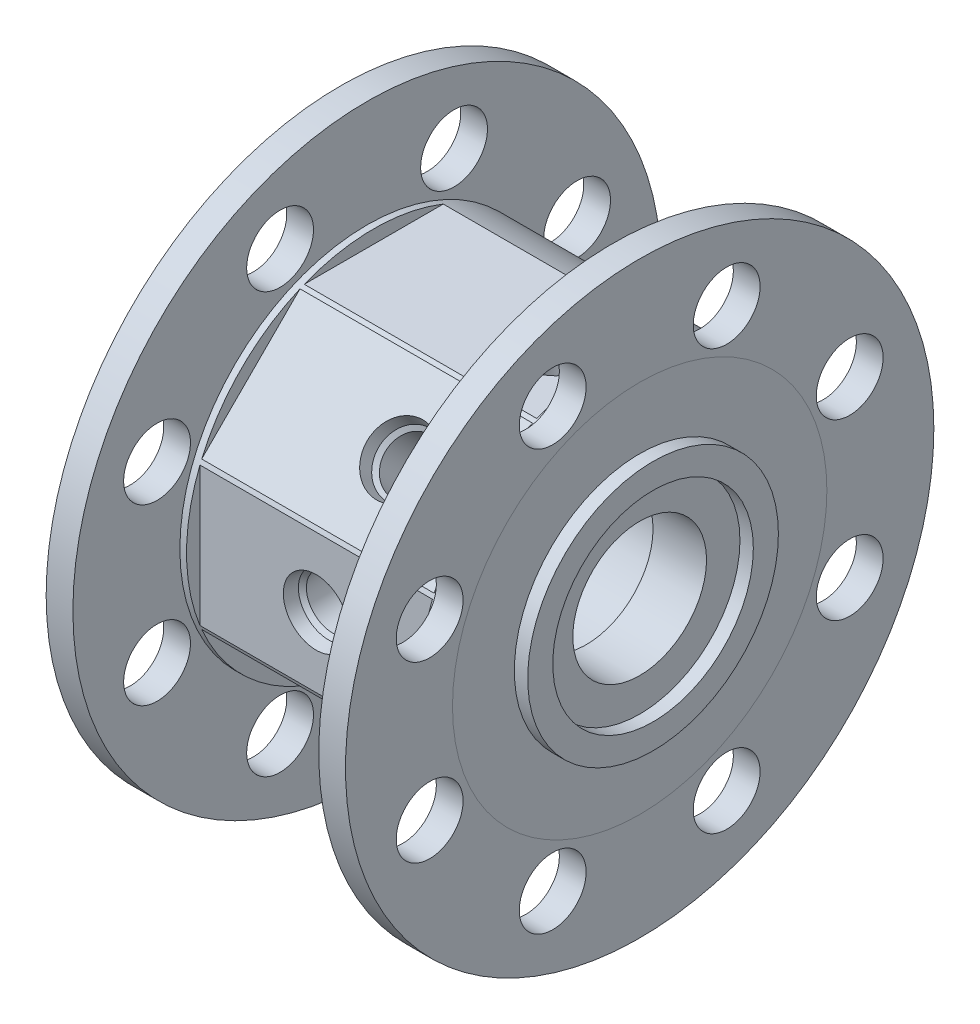
SolidWorks part; units mm, degrees
ref_plane "Front Plane" through (0, 0, 0) normal (0, 0, 1) x (1, 0, 0)
ref_plane "Top Plane" through (0, 0, 0) normal (0, 1, 0) x (1, 0, 0)
ref_plane "Right Plane" through (0, 0, 0) normal (1, 0, 0) x (0, 0, -1)
sketch "Sketch1" plane through (0, 0, 0) normal (0, 0, 1) x (1, 0, 0)
  line L3 (46.703, 15.24) -> (10, 15.24)
  line L4 (10, 15.24) -> (10, 16)
  line L5 (10, 16) -> (0, 16)
  line L8 (0, 16) -> (0, 35.56)
  line L9 (0, 0) -> (-13.7314, 0) construction
  line L11 (46.703, 15.24) -> (46.703, 12.7)
  line L12 (46.703, 12.7) -> (56.863, 12.7)
  line L13 (56.863, 12.7) -> (56.863, 35.56)
  line L15 (0, 35.56) -> (56.863, 35.56)
  dimension "D2" = 36.703
  dimension "D3" = 15.24
  dimension "D4" = 16
  dimension "D5" = 10
  dimension "D1" = 12.7
  dimension "D6" = 10.16
  dimension "D7" = 35.56
revolve "Revolve1" add sketch "Sketch1" angle 360 about L9
sketch "Sketch2" plane through (0, 0, 0) normal (-1, 0, 0) x (0, 0, 1)
  circle A0 centre (0, 0) radius 19.05
  circle A1 centre (0, 0) radius 23.8125
  dimension "D1" = 38.1
  dimension "D2" = 4.7625
extrude "lox side heatshrink ring" add sketch "Sketch2" along normal blind 2.54
sketch "Sketch3" plane through (56.863, 0, 0) normal (1, 0, 0) x (0, 0, -1)
  circle A0 centre (0, 0) radius 19.05
  circle A1 centre (0, 0) radius 23.8125
  dimension "D1" = 4.7625
  dimension "D2" = 38.1
extrude "fuel heatshrink ring" add sketch "Sketch3" along normal blind 2.54
sketch "Sketch10" plane through (0, 0, 0) normal (0, 1, 0) x (1, 0, 0)
  line L0 (0, 0) -> (6.35, 0) construction
  line L1 (6.35, 35.56) -> (50.513, 35.56)
  line L2 (6.35, 35.56) -> (6.35, -35.56)
  line L3 (6.35, -35.56) -> (50.513, -35.56)
  line L4 (50.513, 35.56) -> (50.513, -35.56)
  line L5 (0, 35.56) -> (0, -35.56) construction
  line L6 (56.863, -35.56) -> (56.863, 35.56) construction
  dimension "D1" = 6.35
  dimension "D2" = 6.35
  dimension "D3" = 71.12
extrude "Cut-Extrude3" cut sketch "Sketch10" along normal blind 5.08 from offset 33.02
pattern_circular "CirPattern1" count 5 every 45 about axis through (0, 0, 0) along (1, 0, 0) of "Cut-Extrude3"
ref_plane "fuel recycle" through (40.861, 0, 0) normal (-1, 0, 0) x (0, 0, 1)
ref_plane "fuel drain" through (34.638, 0, 0) normal (-1, 0, 0) x (0, 0, 1)
ref_plane "Inert gas" through (28.415, 0, 0) normal (-1, 0, 0) x (0, 0, 1)
ref_plane "lox drain" through (22.192, 0, 0) normal (-1, 0, 0) x (0, 0, 1)
ref_plane "lox recycle" through (15.969, 0, 0) normal (-1, 0, 0) x (0, 0, 1)
sketch "Sketch16" plane through (40.861, 0, 0) normal (-1, 0, 0) x (0, 0, 1)
  line L0 (13.1982, 33.02) -> (-13.1982, 33.02) construction
  line L1 (13.1982, 33.02) -> (-13.1982, 33.02) construction
  line L3 (0, 33.02) -> (-6.223, 33.02)
  line L4 (-6.223, 33.02) -> (-5.7209, 30.6578)
  line L5 (-5.7209, 30.6578) -> (-4.9609, 29.8978)
  line L6 (-4.9609, 29.8978) -> (-4.9609, 19.1262)
  line L7 (-4.9609, 19.1262) -> (-2.159, 17.9656)
  line L9 (-2.159, 17.9656) -> (-2.159, 15.0863)
  line L11 (0, 15.24) -> (0, 33.02)
  circle A0 centre (0, 0) radius 15.24 construction
  circle A1 centre (0, 0) radius 15.24 construction
  arc A2 (-2.159, 15.0863) -> (0, 15.24) centre (0, 0) cw
  point P12 (0, 0)
  point P14 (0, 0)
  dimension "D1" = 17.78
  dimension "D2" = 78
  dimension "D3" = 45
  dimension "D4" = 112.5
  dimension "D5" = 13.8938
  dimension "D6" = 2.159
  dimension "D7" = 4.9609
  dimension "D8" = 2.3622
  dimension "D9" = 6.223
revolve "fuel recycle port" cut sketch "Sketch16" angle 360 about L11
sketch "Sketch18" plane through (34.638, 0, 0) normal (-1, 0, 0) x (0, 0, 1)
  line L0 (23.3487, 23.3487) -> (18.9483, 27.749)
  line L1 (18.9483, 27.749) -> (17.6331, 25.7236)
  line L2 (17.6331, 25.7236) -> (17.6331, 24.6489)
  line L3 (17.6331, 24.6489) -> (10.0164, 17.0322)
  line L4 (10.0164, 17.0322) -> (11.177, 14.2302)
  line L5 (11.177, 14.2302) -> (9.141, 12.1943)
  line L6 (10.7763, 10.7763) -> (23.3487, 23.3487)
  line L7 (14.0161, 32.6812) -> (32.6812, 14.0161) construction
  line L8 (14.0161, 32.6812) -> (32.6812, 14.0161) construction
  line L9 (10.7763, 10.7763) -> (13.6748, 7.8778) construction
  arc A0 (9.141, 12.1943) -> (10.7763, 10.7763) centre (0, 0) cw
  circle A1 centre (0, 0) radius 15.24 construction
  circle A2 centre (0, 0) radius 15.24 construction
  point P16 (23.3487, 23.3487)
  dimension "D1" = 15.24
  dimension "D2" = 78
  dimension "D3" = 45
  dimension "D4" = 112.5
  dimension "D6" = 6.223
  dimension "D9" = 17.78
  dimension "D5" = 13.8938
  dimension "D7" = 2.3622
  dimension "D8" = 4.9609
  dimension "D10" = 2.159
revolve "fuel drain port" cut sketch "Sketch18" angle 360 about L6
sketch "inert point" plane through (28.415, 0, 0) normal (-1, 0, 0) x (0, 0, 1)
  line L0 (33.02, -13.1982) -> (33.02, 13.1982) construction
  line L1 (33.02, -13.1982) -> (33.02, 13.1982) construction
  point P2 (33.02, 0)
sketch "fuel recycle point" plane through (40.861, 0, 0) normal (-1, 0, 0) x (0, 0, 1)
  line L0 (13.1982, 33.02) -> (-13.1982, 33.02) construction
  line L1 (13.1982, 33.02) -> (-13.1982, 33.02) construction
  point P2 (0, 33.02)
sketch "fuel drain point" plane through (34.638, 0, 0) normal (-1, 0, 0) x (0, 0, 1)
  line L0 (32.6812, 14.0161) -> (14.0161, 32.6812) construction
  line L1 (32.6812, 14.0161) -> (14.0161, 32.6812) construction
  point P2 (23.3487, 23.3487)
sketch "lox drain point" plane through (22.192, 0, 0) normal (-1, 0, 0) x (0, 0, 1)
  line L0 (14.0161, -32.6812) -> (32.6812, -14.0161) construction
  line L1 (14.0161, -32.6812) -> (32.6812, -14.0161) construction
  point P2 (23.3487, -23.3487)
sketch "lox recycle point" plane through (15.969, 0, 0) normal (-1, 0, 0) x (0, 0, 1)
  line L0 (-13.1982, -33.02) -> (13.1982, -33.02) construction
  line L1 (-13.1982, -33.02) -> (13.1982, -33.02) construction
  point P2 (0, -33.02)
  point P7 (0, 0)
sketch3d "3DSketch1"
  point P0 (22.192, -23.3487, 23.3487)
  point P1 (15.969, -33.02, 0)
  point P3 (28.415, 0, 33.02)
  point P5 (34.638, 23.3487, 23.3487)
  point P7 (40.861, 33.02, 0)
sketch "Sketch34" plane through (28.415, 0, 0) normal (-1, 0, 0) x (0, 0, 1)
  line L0 (33.02, 0) -> (33.02, 6.223)
  line L1 (33.02, 6.223) -> (30.6578, 5.7209)
  line L2 (30.6578, 5.7209) -> (29.8978, 4.9609)
  line L3 (29.8978, 4.9609) -> (19.1262, 4.9609)
  line L4 (19.1262, 4.9609) -> (17.9656, 2.159)
  line L5 (17.9656, 2.159) -> (15.0863, 2.159)
  line L6 (15.24, 0) -> (33.02, 0)
  line L7 (33.02, -13.1982) -> (33.02, 13.1982) construction
  line L8 (15.24, 0) -> (15.24, -4.0992) construction
  arc A0 (15.0863, 2.159) -> (15.24, 0) centre (0, 0) cw
  point P9 (0, 0)
  dimension "D5" = 15.24
  dimension "D1" = 78
  dimension "D2" = 45
  dimension "D3" = 112.5
  dimension "D4" = 6.223
  dimension "D6" = 17.78
  dimension "D7" = 13.8938
  dimension "D8" = 2.3622
  dimension "D9" = 4.9609
  dimension "D10" = 2.159
revolve "Cut-Revolve3" cut sketch "Sketch34" angle 360 about L6
sketch "Sketch35" plane through (22.192, 0, 0) normal (-1, 0, 0) x (0, 0, 1)
  line L0 (23.3487, -23.3487) -> (27.749, -18.9483)
  line L1 (27.749, -18.9483) -> (25.7236, -17.6331)
  line L2 (25.7236, -17.6331) -> (24.6489, -17.6331)
  line L3 (24.6489, -17.6331) -> (17.0322, -10.0164)
  line L4 (17.0322, -10.0164) -> (14.2302, -11.177)
  line L5 (14.2302, -11.177) -> (12.1943, -9.141)
  line L6 (10.7763, -10.7763) -> (23.3487, -23.3487)
  line L7 (14.0161, -32.6812) -> (32.6812, -14.0161) construction
  line L8 (10.7763, -10.7763) -> (7.8778, -13.6748) construction
  arc A0 (12.1943, -9.141) -> (10.7763, -10.7763) centre (0, 0) cw
  point P9 (0, 0)
  point P10 (0, 0)
  dimension "D5" = 15.24
  dimension "D1" = 78
  dimension "D2" = 45
  dimension "D3" = 112.5
  dimension "D4" = 6.223
  dimension "D6" = 17.78
  dimension "D7" = 13.8938
  dimension "D8" = 2.3622
  dimension "D9" = 4.9609
  dimension "D10" = 2.159
revolve "Cut-Revolve4" cut sketch "Sketch35" angle 360 about L6
sketch "Sketch36" plane through (15.969, 0, 0) normal (-1, 0, 0) x (0, 0, 1)
  line L0 (0, -33.02) -> (6.223, -33.02)
  line L1 (6.223, -33.02) -> (5.7209, -30.6578)
  line L2 (5.7209, -30.6578) -> (4.9609, -29.8978)
  line L3 (4.9609, -29.8978) -> (4.9609, -19.1262)
  line L4 (4.9609, -19.1262) -> (2.159, -17.9656)
  line L5 (2.159, -17.9656) -> (2.159, -15.0863)
  line L6 (0, -15.24) -> (0, -33.02)
  line L7 (-13.1982, -33.02) -> (13.1982, -33.02) construction
  line L8 (0, -15.24) -> (-4.0992, -15.24) construction
  arc A0 (2.159, -15.0863) -> (0, -15.24) centre (0, 0) cw
  point P9 (0, 0)
  point P10 (0, 0)
  dimension "D5" = 15.24
  dimension "D1" = 78
  dimension "D2" = 45
  dimension "D3" = 112.5
  dimension "D4" = 6.223
  dimension "D6" = 17.78
  dimension "D7" = 13.8938
  dimension "D8" = 2.3622
  dimension "D9" = 4.9609
  dimension "D10" = 2.159
  dimension "D11" = 6.223
  dimension "D12" = 0
revolve "Cut-Revolve5" cut sketch "Sketch36" angle 360 about L6
sketch "Sketch37" plane through (56.863, 0, 0) normal (1, 0, 0) x (0, 0, -1)
  circle A0 centre (0, 0) radius 55.88
  circle A1 centre (0, 0) radius 35.56 construction
  circle A2 centre (0, 0) radius 35.56
  dimension "D1" = 111.76
extrude "Boss-Extrude1" add sketch "Sketch37" against normal blind 5.08 separate body
sketch "Sketch38" plane through (0, 0, 0) normal (-1, 0, 0) x (0, 0, 1)
  circle A0 centre (0, 0) radius 55.88
  circle A1 centre (0, 0) radius 35.56 construction
  circle A2 centre (0, 0) radius 35.56
extrude "Boss-Extrude2" add sketch "Sketch38" against normal blind 5.08
sketch "Sketch39" plane through (0, 0, 0) normal (-1, 0, 0) x (0, 0, 1)
  line L0 (0, 0) -> (16.5243, 39.8931) construction
  line L1 (0, 0) -> (0, 27.0765) construction
  circle A0 centre (0, 0) radius 55.88 construction
  point P0 (16.5243, 39.8931)
  point P6 (0, 27.0765)
  dimension "D1" = 43.18
  dimension "D2" = 22.5
sketch "Sketch40" plane through (0, 0, 0) normal (-1, 0, 0) x (0, 0, 1)
  point P0 (16.5243, 39.8931)
hole_wizard "1/2 (0.5) Diameter Hole1" positions "Sketch40" profile "Sketch41" hole size "1/2" standard "ANSI Inch"
sketch "Sketch41" plane through (0, 39.8931, 16.5243) normal (0, 1, 0) x (0, 0, 1)
  line L0 (0, 0) -> (0, 8.8955)
  line L1 (0, 8.8955) -> (6.35, 5.08)
  line L2 (6.35, 5.08) -> (6.35, 0)
  line L5 (6.35, 0) -> (0, 0)
  line L10 (0, 8.8955) -> (-6.35, 5.08) construction
  line L11 (0, -6.35) -> (0, 107.95) construction
  dimension "Hole Dia." = 12.7
  dimension "Hole Depth" = 5.08
  dimension "Drill Angle" = 118
pattern_circular "CirPattern2" count 8 over 360 about axis through (0, 0, 0) along (1, 0, 0) of "1/2 (0.5) Diameter Hole1"
sketch "Sketch42" plane through (56.863, 0, 0) normal (1, 0, 0) x (0, 0, -1)
  line L0 (0, 0) -> (0, 42.6249) construction
  line L1 (0, 0) -> (-16.5243, 39.8931) construction
  point P5 (-16.5243, 39.8931)
  dimension "D2" = 22.5
  dimension "D1" = 42.6249
  dimension "D3" = 43.18
hole_wizard "1/2 (0.5) Diameter Hole2" positions "Sketch42" profile "Sketch43" hole size "1/2" standard "ANSI Inch"
sketch "Sketch43" plane through (56.863, 39.8931, 16.5243) normal (0, 1, 0) x (0, 0, -1)
  line L0 (0, 0) -> (0, 8.8955)
  line L1 (0, 8.8955) -> (6.35, 5.08)
  line L2 (6.35, 5.08) -> (6.35, 0)
  line L5 (6.35, 0) -> (0, 0)
  line L10 (0, 8.8955) -> (-6.35, 5.08) construction
  line L11 (0, -6.35) -> (0, 107.95) construction
  dimension "Hole Dia." = 12.7
  dimension "Hole Depth" = 5.08
  dimension "Drill Angle" = 118
pattern_circular "CirPattern3" count 8 over 360 about axis through (0, 0, 0) along (1, 0, 0) of "1/2 (0.5) Diameter Hole2"
equation "\"bearing_radius\"= 0.629921"
equation "\"bearing_width\"=0.393701"
equation "\"kero_radius\"=0.23622in"
equation "\"lox_radius\"=0.23622in"
equation "\"Cavity_width\"=0.031in"
equation "\"tooth_width\"=0.01in"
equation "\"cavity_depth\"=0.031in"
equation "\"seal_step\"=0.01in"
equation "\"purge_length\"=0.04in"
equation "\"insert_radius\" = 0.6in"
equation "\"recycle_groove width\" = 0.06in"
equation "\"recycle_groove_depth\" = 0.06in"
equation "\"N2_purge_width\"= .06in"
equation "\"N2_purge_depth\"= .06in"
equation "\"drain_width\"= .06in"
equation "\"drain_depth\"= .06in"
equation "\"radial_clearance\"= .002in"
equation "\"IPS_flange_width\"= .2in"
equation "\"IPS_flange_radius\" = 2.2in"
equation "\"IPS_LOX_male_radius\"= .9in"
equation "\"IPS_Kero_male_radius\" = .9in"
equation "\"IPS_radius\"= 1.4in"
equation "\"InsertLength\"= 1.445in"
equation "\"lox_in_radius\"=.375in"
equation "\"D3@Sketch1\"=\"insert_radius\""
equation "\"D5@Sketch1\"=\"bearing_width\""
equation "\"D4@Sketch1\"=\"bearing_radius\""
equation "\"D2@Sketch1\"=\"InsertLength\""
equation "\"D1\" = \"IPS_flange_radius\" * 2"
equation "\"D1\" = \"IPS_flange_width\""
equation "\"D1@Sketch10\"=\"IPS_flange_width\"+.05in"
equation "\"D2@Sketch10\"=\"IPS_flange_width\"+.05in"
equation "\"D3@Sketch10\"=\"IPS_radius\"*2"
equation "\"D19@Cut-Extrude3\"=\"IPS_radius\"-.1in"
equation "\"D7@Sketch1\"=\"IPS_radius\""
equation "\"D1@Sketch18\"=\"insert_radius\""
equation "\"D9@Sketch18\"=\"IPS_radius\"-\"insert_radius\"-.1in"
equation "\"D1@Sketch37\"=\"IPS_flange_radius\"*2"
equation "\"D1@Sketch39\"=\"IPS_flange_radius\"-.5in"
equation "\"Lox_bolt_offset\"= 22.5deg"
equation "\"D2@Sketch39\"=\"Lox_bolt_offset\""
equation "\"fuel_bolt_ofset\"= 22.5deg"
equation "\"D2@Sketch42\"=\"fuel_bolt_ofset\""
equation "\"D3@Sketch42\"=\"IPS_flange_radius\"-.5in"
